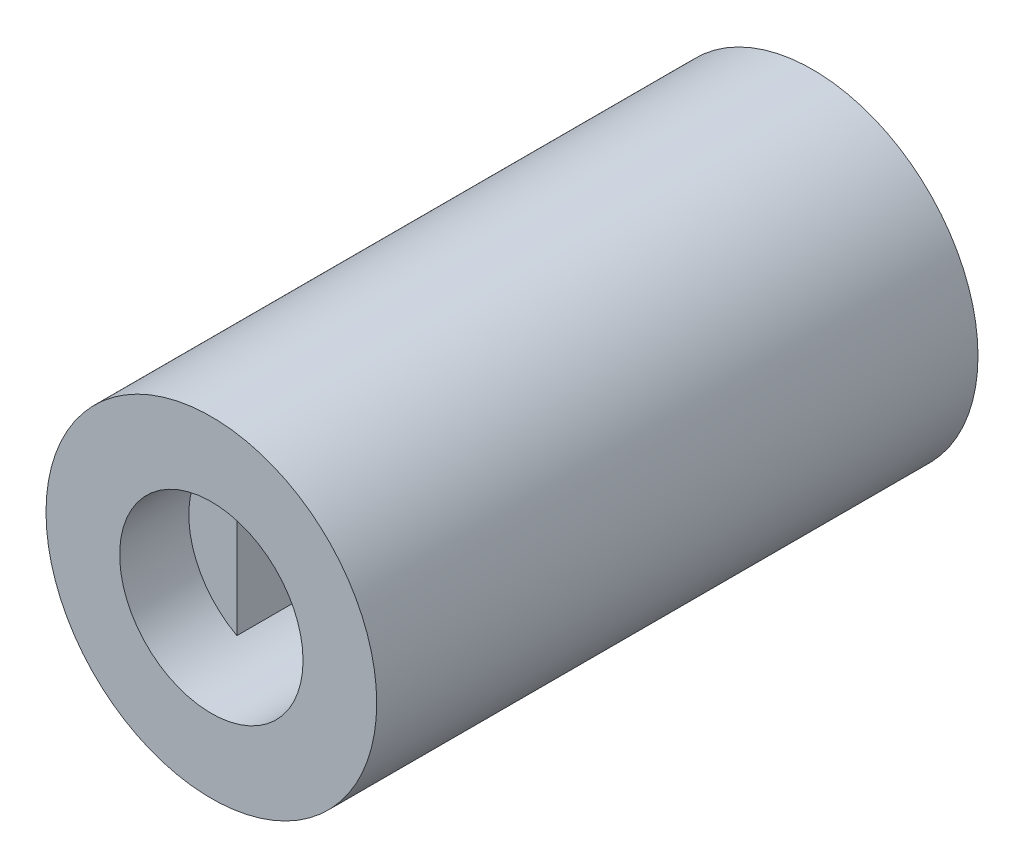
SolidWorks part; units mm, degrees
ref_plane "Front Plane" through (0, 0, 0) normal (0, 0, 1) x (1, 0, 0)
ref_plane "Top Plane" through (0, 0, 0) normal (0, 1, 0) x (1, 0, 0)
ref_plane "Right Plane" through (0, 0, 0) normal (1, 0, 0) x (0, 0, -1)
sketch "Sketch1" plane through (0, 0, 0) normal (0, 0, 1) x (1, 0, 0)
  circle A0 centre (0, 0) radius 5.5
  dimension "D1" = 11
extrude "Boss-Extrude1" add sketch "Sketch1" along normal blind 20
sketch "Sketch2" plane through (0, 0, 20) normal (0, 0, 1) x (1, 0, 0)
  line L0 (3.05, 0) -> (-1.45, 0) construction
  line L1 (-1.45, 0) -> (-1.45, 2.6833)
  line L2 (-1.45, 2.6833) -> (-1.45, -2.6833)
  line L3 (3.05, 0) -> (-1.45, 0)
  circle A0 centre (0, 0) radius 3.05
  dimension "D1" = 6.1
  dimension "D2" = 4.5
extrude "Cut-Extrude1" cut sketch "Sketch2" against normal blind 12 contours L0 A0 L1 | A0 L0 L2
sketch "Sketch3" plane through (0, 0, 0) normal (0, 0, -1) x (-1, 0, 0)
  line L0 (0, 0) -> (2.3, 0) construction
  line L1 (2.3, 2.0785) -> (2.3, -2.0785)
  line L2 (0, 0) -> (0, -0.8782) construction
  line L3 (-2.3, 2.0785) -> (-2.3, -2.0785)
  circle A0 centre (0, 0) radius 3.1
  dimension "D1" = 6.2
  dimension "D2" = 2.3
extrude "Cut-Extrude2" cut sketch "Sketch3" against normal blind 7.8 contours L1 A0 L3
sketch "Sketch4" plane through (0, 0, 20) normal (0, 0, 1) x (1, 0, 0)
  circle A0 centre (0, 0) radius 3.05
extrude "Cut-Extrude3" cut sketch "Sketch4" against normal blind 2.3
